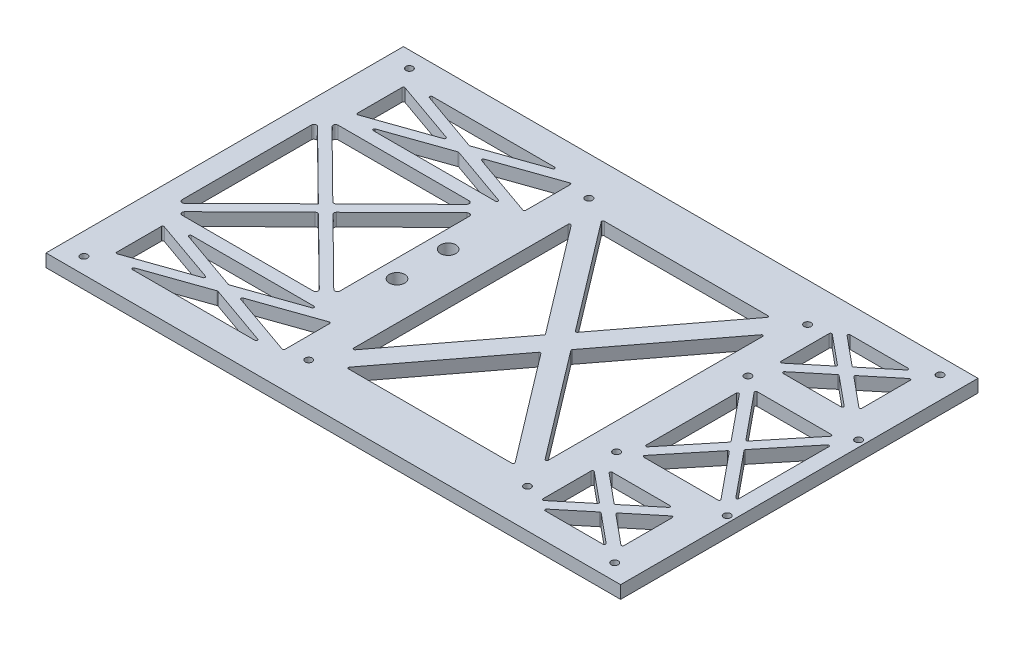
SolidWorks part; units mm, degrees
ref_plane "Front" through (0, 0, 0) normal (0, 0, 1) x (1, 0, 0)
ref_plane "Top" through (0, 0, 0) normal (0, 1, 0) x (1, 0, 0)
ref_plane "Right" through (0, 0, 0) normal (1, 0, 0) x (0, 0, -1)
sketch "batteryPackMountingHolesSketch" plane through (0, 0, 0) normal (0, 1, 0) x (1, 0, 0)
  line L0 (46, 0) -> (46, 116) construction
  line L1 (0, 0) -> (92, 0) construction
  line L2 (0, 0) -> (0, 116) construction
  line L3 (0, 116) -> (92, 116) construction
  line L4 (92, 0) -> (92, 116) construction
  line L5 (0, 58) -> (92, 58) construction
  circle A0 centre (3.25, 112.75) radius 1.375
  circle A1 centre (3.25, 3.25) radius 1.375
  circle A2 centre (88.75, 112.75) radius 1.375
  circle A3 centre (88.75, 3.25) radius 1.375
  dimension "D3" = 2.75
  dimension "D1" = 116
  dimension "D2" = 92
  dimension "D4" = 3.25
  dimension "D5" = 3.25
sketch "9VbatteryMountingHolesSketch" plane through (0, 0, 0) normal (0, 1, 0) x (1, 0, 0)
  line L0 (0, 58) -> (92, 58) construction
  line L1 (92, 28.575) -> (140.25, 28.575) construction
  line L2 (92, 28.575) -> (92, 87.425) construction
  line L3 (92, 87.425) -> (140.25, 87.425) construction
  line L4 (140.25, 28.575) -> (140.25, 87.425) construction
  line L5 (116.125, 28.575) -> (116.125, 87.425) construction
  line L6 (92, 58) -> (140.25, 58) construction
  line L7 (92, 0) -> (92, 116) construction
  circle A0 centre (94.5, 83.675) radius 1.375
  circle A1 centre (137.75, 83.675) radius 1.375
  circle A2 centre (94.5, 32.325) radius 1.375
  circle A3 centre (137.75, 32.325) radius 1.375
  point P5 (92, 58)
  dimension "D3" = 2.75
  dimension "D1" = 48.25
  dimension "D2" = 58.85
  dimension "D4" = 3.75
  dimension "D5" = 2.5
sketch "dualSwitchMountingHolesSketch" plane through (0, 0, 0) normal (0, 1, 0) x (1, 0, 0)
  line L0 (-7, 68) -> (-7, 48) construction
  line L1 (0, 58) -> (-14, 58) construction
  line L2 (-14, 77) -> (0, 77) construction
  line L3 (-14, 77) -> (-14, 39) construction
  line L4 (-14, 39) -> (0, 39) construction
  line L5 (0, 77) -> (0, 39) construction
  line L6 (0, 58) -> (92, 58) construction
  line L7 (0, 0) -> (0, 116) construction
  circle A0 centre (-7, 68) radius 3
  circle A1 centre (-7, 48) radius 3
  point P8 (-7, 58)
  point P11 (-7, 58)
  dimension "D1" = 6
  dimension "D2" = 20
  dimension "D3" = 14
  dimension "D4" = 9
sketch "Sketch4" plane through (0, 0, 0) normal (0, 1, 0) x (1, 0, 0)
  line L0 (-84.34, 58) -> (140.25, 58) construction
  line L1 (-84.34, -11.85) -> (140.25, -11.85)
  line L2 (-84.34, -11.85) -> (-84.34, 127.85)
  line L3 (-84.34, 127.85) -> (140.25, 127.85)
  line L4 (140.25, -11.85) -> (140.25, 127.85)
  line L5 (0, 58) -> (92, 58) construction
  line L6 (140.25, 28.575) -> (140.25, 87.425) construction
  dimension "D1" = 224.59
  dimension "D2" = 139.7
extrude "topChassisBase" add sketch "Sketch4" along normal blind 5
extrude "batteryPackMountingHoles" cut sketch "batteryPackMountingHolesSketch" along normal blind 7.5
extrude "9VbatteryMountingHoles" cut sketch "9VbatteryMountingHolesSketch" along normal blind 7.5
extrude "dualSwitchMountingHoles" cut sketch "dualSwitchMountingHolesSketch" along normal blind 7.5
sketch "Sketch5" plane through (0, 5, 0) normal (0, 1, 0) x (1, 0, 0)
  line L0 (-84.34, 58) -> (140.25, 58) construction
  line L1 (-84.34, 127.85) -> (-84.34, -11.85) construction
  line L2 (140.25, -11.85) -> (140.25, 127.85) construction
  line L3 (27.955, -11.85) -> (27.955, 127.85) construction
  line L4 (-84.34, -11.85) -> (140.25, -11.85) construction
  line L5 (140.25, 127.85) -> (-84.34, 127.85) construction
  circle A0 centre (-75.7725, 121.6) radius 1.375
  circle A1 centre (131.6825, 121.6) radius 1.375
  circle A2 centre (-75.7725, -5.6) radius 1.375
  circle A3 centre (131.6825, -5.6) radius 1.375
  dimension "D1" = 2.75
  dimension "D2" = 6.25
  dimension "D3" = 8.5675
extrude "bottomChassisMountingHoles" cut sketch "Sketch5" against normal through all
sketch "Sketch7" plane through (0, 5, 0) normal (0, 1, 0) x (1, 0, 0)
  line L0 (8.8981, 100.2077) -> (40.746, 58.3025)
  line L1 (13.634, 8.8025) -> (45.6019, 50.8655)
  line L2 (13.634, 107.1975) -> (45.6019, 65.1345)
  line L3 (8.8981, 15.7923) -> (40.746, 57.6975)
  line L4 (11.1846, 110.4203) -> (87.1846, 10.4203) construction
  line L5 (4.8154, 105.5797) -> (80.8154, 5.5797) construction
  line L6 (11.1846, 5.5797) -> (87.1846, 105.5797) construction
  line L7 (4.8154, 10.4203) -> (80.8154, 110.4203) construction
  line L8 (46.3981, 65.1345) -> (78.366, 107.1975)
  line L9 (46.3981, 50.8655) -> (78.366, 8.8025)
  line L10 (51.254, 57.6975) -> (83.1019, 15.7923)
  line L11 (51.254, 58.3025) -> (83.1019, 100.2077)
  line L12 (-7, 68) -> (-7, 48) construction
  line L13 (94.5, 83.675) -> (137.75, 83.675) construction
  line L14 (8, 108) -> (84, 8) construction
  line L15 (8, 8) -> (84, 108) construction
  line L16 (94.5, 83.675) -> (94.5, 32.325) construction
  line L17 (94.5, 32.325) -> (137.75, 32.325) construction
  line L18 (8, 8) -> (84, 8)
  line L19 (84, 8) -> (84, 108)
  line L20 (8, 108) -> (8, 8)
  line L21 (84, 108) -> (8, 108)
  line L22 (14.0321, 8) -> (77.9679, 8)
  line L23 (84, 16.0949) -> (84, 99.9051)
  line L24 (8, 99.9051) -> (8, 16.0949)
  line L25 (77.9679, 108) -> (14.0321, 108)
  line L26 (137.75, 83.675) -> (137.75, 32.325) construction
  line L28 (101.6375, 80.175) -> (130.6125, 80.175)
  line L29 (134.25, 75.6129) -> (134.25, 40.3871)
  line L30 (101.6375, 35.825) -> (130.6125, 35.825)
  line L31 (98, 75.6129) -> (98, 40.3871)
  line L32 (98, 80.175) -> (134.25, 35.825) construction
  line L33 (98, 35.825) -> (134.25, 80.175) construction
  line L34 (98.8871, 75.9294) -> (113.2833, 58.3164)
  line L35 (101.2504, 36.6414) -> (115.7379, 54.3661)
  line L36 (101.2504, 79.3586) -> (115.7379, 61.6339)
  line L37 (98.8871, 40.0706) -> (113.2833, 57.6836)
  line L38 (99.5485, 81.4407) -> (135.7985, 37.0907) construction
  line L39 (98, 80.175) -> (134.25, 80.175) construction
  line L40 (98, 80.175) -> (98, 35.825) construction
  line L41 (96.4515, 78.9093) -> (132.7015, 34.5593) construction
  line L42 (96.4515, 37.0907) -> (132.7015, 81.4407) construction
  line L43 (98, 35.825) -> (134.25, 35.825) construction
  line L44 (99.5485, 34.5593) -> (135.7985, 78.9093) construction
  line L45 (134.25, 80.175) -> (134.25, 35.825) construction
  line L46 (116.5121, 61.6339) -> (130.9996, 79.3586)
  line L47 (116.5121, 54.3661) -> (130.9996, 36.6414)
  line L48 (118.9667, 58.3164) -> (133.3629, 75.9294)
  line L49 (118.9667, 57.6836) -> (133.3629, 40.0706)
  line L50 (92, 87.425) -> (140.25, 87.425) construction
  line L51 (131.6825, 121.6) -> (92, 121.6) construction
  line L52 (131.6825, 121.6) -> (131.6825, 87.425) construction
  line L53 (131.6825, 87.425) -> (92, 87.425) construction
  line L54 (92, 121.6) -> (92, 87.425) construction
  line L55 (92, 0) -> (92, 116) construction
  line L56 (-84.34, 58) -> (-125.8248, 58) construction
  line L57 (123.1521, 117.6) -> (100.5304, 117.6)
  line L58 (96, 113.9441) -> (96, 95.0809)
  line L59 (123.1521, 91.425) -> (100.5304, 91.425)
  line L60 (127.6825, 113.9441) -> (127.6825, 95.0809)
  line L61 (96, 117.6) -> (127.6825, 91.425) construction
  line L62 (96, 91.425) -> (127.6825, 117.6) construction
  line L63 (96.8185, 114.3296) -> (108.2346, 104.898)
  line L64 (100.2119, 92.3105) -> (111.5228, 101.6551)
  line L65 (100.2119, 116.7145) -> (111.5228, 107.3699)
  line L66 (96.8185, 94.6954) -> (108.2346, 104.127)
  line L67 (94.7262, 92.9669) -> (126.4087, 119.1419) construction
  line L68 (96, 117.6) -> (96, 91.425) construction
  line L69 (127.6825, 91.425) -> (96, 91.425) construction
  line L70 (97.2738, 89.8831) -> (128.9563, 116.0581) construction
  line L71 (94.7262, 116.0581) -> (126.4087, 89.8831) construction
  line L72 (127.6825, 117.6) -> (127.6825, 91.425) construction
  line L73 (97.2738, 119.1419) -> (128.9563, 92.9669) construction
  line L74 (127.6825, 117.6) -> (96, 117.6) construction
  line L75 (115.4479, 104.898) -> (126.864, 114.3296)
  line L76 (115.4479, 104.127) -> (126.864, 94.6954)
  line L77 (112.1597, 107.3699) -> (123.4706, 116.7145)
  line L78 (112.1597, 101.6551) -> (123.4706, 92.3105)
  line L79 (115.4479, 11.102) -> (126.864, 1.6704)
  line L80 (115.4479, 11.873) -> (126.864, 21.3046)
  line L81 (127.6825, 2.0559) -> (127.6825, 20.9191)
  line L82 (100.2119, 23.6895) -> (111.5228, 14.3449)
  line L83 (123.1521, 24.575) -> (100.5304, 24.575)
  line L84 (112.1597, 14.3449) -> (123.4706, 23.6895)
  line L85 (96.8185, 1.6704) -> (108.2346, 11.102)
  line L86 (96.8185, 21.3046) -> (108.2346, 11.873)
  line L87 (96, 2.0559) -> (96, 20.9191)
  line L88 (123.1521, -1.6) -> (100.5304, -1.6)
  line L89 (112.1597, 8.6301) -> (123.4706, -0.7145)
  line L90 (100.2119, -0.7145) -> (111.5228, 8.6301)
  line L91 (-75.7725, 88.5) -> (-14, 88.5) construction
  line L92 (-75.7725, -5.6) -> (0, -5.6) construction
  line L93 (-75.7725, -5.6) -> (-75.7725, 27.5) construction
  line L95 (0, -5.6) -> (0, 27.5) construction
  line L96 (0, 0) -> (0, 116) construction
  line L97 (-5, 2.2253) -> (-5, 19.6747)
  line L98 (-61.8044, 22.5) -> (-13.9681, 22.5)
  line L99 (-70.7725, 2.2253) -> (-70.7725, 19.6747)
  line L100 (-61.8044, -0.6) -> (-13.9681, -0.6)
  line L101 (-70.7725, 22.5) -> (-5, -0.6) construction
  line L102 (-70.7725, -0.6) -> (-5, 22.5) construction
  line L103 (-70.1068, 20.1464) -> (-45.2651, 11.4218)
  line L104 (-61.97, 0.3718) -> (-38.0519, 8.772)
  line L105 (-61.97, 21.5282) -> (-38.0519, 13.128)
  line L106 (-70.1068, 1.7536) -> (-45.2651, 10.4782)
  line L107 (-70.1098, 24.387) -> (-4.3373, 1.287) construction
  line L108 (-70.7725, 22.5) -> (-5, 22.5) construction
  line L109 (-71.4352, 20.613) -> (-5.6627, -2.487) construction
  line L110 (-70.7725, -0.6) -> (-70.7725, 22.5) construction
  line L111 (-71.4352, 1.287) -> (-5.6627, 24.387) construction
  line L112 (-70.1098, -2.487) -> (-4.3373, 20.613) construction
  line L113 (-70.7725, -0.6) -> (-5, -0.6) construction
  line L114 (-5, -0.6) -> (-5, 22.5) construction
  line L115 (-37.7206, 13.128) -> (-13.8025, 21.5282)
  line L116 (-37.7206, 8.772) -> (-13.8025, 0.3718)
  line L117 (-30.5074, 10.4782) -> (-5.6657, 1.7536)
  line L118 (-30.5074, 11.4218) -> (-5.6657, 20.1464)
  line L119 (-61.97, 115.6282) -> (-38.0519, 107.228)
  line L120 (-37.7206, 107.228) -> (-13.8025, 115.6282)
  line L121 (-61.8044, 116.6) -> (-13.9681, 116.6)
  line L122 (-30.5074, 104.5782) -> (-5.6657, 95.8536)
  line L123 (-5, 113.7747) -> (-5, 96.3253)
  line L124 (-30.5074, 105.5218) -> (-5.6657, 114.2464)
  line L125 (-61.97, 94.4718) -> (-38.0519, 102.872)
  line L126 (-61.8044, 93.5) -> (-13.9681, 93.5)
  line L127 (-37.7206, 102.872) -> (-13.8025, 94.4718)
  line L128 (-70.1068, 114.2464) -> (-45.2651, 105.5218)
  line L129 (-70.1068, 95.8536) -> (-45.2651, 104.5782)
  line L130 (-70.7725, 113.7747) -> (-70.7725, 96.3253)
  line L138 (0, 88.5) -> (-75.7725, 88.5) construction
  line L139 (-75.7725, 27.5) -> (0, 27.5) construction
  line L144 (0, 27.5) -> (-75.7725, 27.5) construction
  line L145 (-75.7725, 88.5) -> (-75.7725, 27.5) construction
  line L146 (-75.7725, 27.5) -> (-14, 27.5) construction
  line L147 (-14, 88.5) -> (-14, 27.5) construction
  line L148 (-14, 88.5) -> (-75.7725, 27.5) construction
  line L149 (-75.7725, 88.5) -> (-14, 27.5) construction
  line L150 (-18.5796, 86.7885) -> (-44.1836, 61.5047)
  line L151 (-74.0699, 84.0079) -> (-47.7326, 58)
  line L155 (-15.7026, 84.0079) -> (-41.3193, 58.7115)
  line L156 (-71.1929, 86.7885) -> (-45.5889, 61.5047)
  line L158 (-75.7725, 121.6) -> (-75.7725, 88.5) construction
  line L160 (-75.7725, 121.6) -> (0, 121.6) construction
  line L161 (0, 121.6) -> (0, 88.5) construction
  line L162 (-19.2823, 88.5) -> (-70.4902, 88.5)
  line L163 (-75.7725, 83.2963) -> (-75.7725, 32.7037)
  line L164 (-70.4902, 27.5) -> (-19.2823, 27.5)
  line L166 (-14, 83.2963) -> (-14, 32.7037)
  line L168 (-15.4053, 89.9231) -> (-77.1778, 28.9231) construction
  line L169 (-12.5947, 87.0769) -> (-74.3672, 26.0769) construction
  line L170 (-74.3672, 89.9231) -> (-12.5947, 28.9231) construction
  line L171 (-77.1778, 87.0769) -> (-15.4053, 26.0769) construction
  line L172 (-41.3193, 57.2885) -> (-15.7026, 31.9921)
  line L173 (-47.7326, 58) -> (-74.0699, 31.9921)
  line L174 (-45.5889, 54.4953) -> (-71.1929, 29.2115)
  line L175 (-44.1836, 54.4953) -> (-18.5796, 29.2115)
  arc A0 (96.8185, 114.3296) -> (96, 113.9441) centre (96.5, 113.9441) ccw
  arc A1 (108.2346, 104.898) -> (108.2346, 104.127) centre (107.9161, 104.5125) cw
  arc A2 (123.4706, 116.7145) -> (123.1521, 117.6) centre (123.1521, 117.1) ccw
  arc A3 (100.2119, 116.7145) -> (100.5304, 117.6) centre (100.5304, 117.1) cw
  arc A4 (111.5228, 107.3699) -> (112.1597, 107.3699) centre (111.8413, 107.7553) ccw
  arc A5 (126.864, 114.3296) -> (127.6825, 113.9441) centre (127.1825, 113.9441) cw
  arc A6 (115.4479, 104.898) -> (115.4479, 104.127) centre (115.7664, 104.5125) ccw
  arc A7 (127.6825, 95.0809) -> (126.864, 94.6954) centre (127.1825, 95.0809) cw
  arc A8 (123.4706, 92.3105) -> (123.1521, 91.425) centre (123.1521, 91.925) cw
  arc A9 (112.1597, 101.6551) -> (111.5228, 101.6551) centre (111.8413, 101.2697) ccw
  arc A10 (100.5304, 91.425) -> (100.2119, 92.3105) centre (100.5304, 91.925) cw
  arc A11 (96.8185, 94.6954) -> (96, 95.0809) centre (96.5, 95.0809) cw
  arc A12 (115.4479, 11.102) -> (115.4479, 11.873) centre (115.7664, 11.4875) cw
  arc A13 (126.864, 1.6704) -> (127.6825, 2.0559) centre (127.1825, 2.0559) ccw
  arc A14 (127.6825, 20.9191) -> (126.864, 21.3046) centre (127.1825, 20.9191) ccw
  arc A15 (100.5304, 24.575) -> (100.2119, 23.6895) centre (100.5304, 24.075) ccw
  arc A16 (123.4706, 23.6895) -> (123.1521, 24.575) centre (123.1521, 24.075) ccw
  arc A17 (112.1597, 14.3449) -> (111.5228, 14.3449) centre (111.8413, 14.7303) cw
  arc A18 (108.2346, 11.102) -> (108.2346, 11.873) centre (107.9161, 11.4875) ccw
  arc A19 (96.8185, 1.6704) -> (96, 2.0559) centre (96.5, 2.0559) cw
  arc A20 (96.8185, 21.3046) -> (96, 20.9191) centre (96.5, 20.9191) ccw
  arc A21 (123.4706, -0.7145) -> (123.1521, -1.6) centre (123.1521, -1.1) cw
  arc A22 (100.2119, -0.7145) -> (100.5304, -1.6) centre (100.5304, -1.1) ccw
  arc A23 (111.5228, 8.6301) -> (112.1597, 8.6301) centre (111.8413, 8.2447) cw
  arc A24 (98, 75.6129) -> (98.8871, 75.9294) centre (98.5, 75.6129) cw
  arc A25 (113.2833, 57.6836) -> (113.2833, 58.3164) centre (112.8961, 58) ccw
  arc A26 (98.8871, 40.0706) -> (98, 40.3871) centre (98.5, 40.3871) cw
  arc A27 (101.2504, 79.3586) -> (101.6375, 80.175) centre (101.6375, 79.675) cw
  arc A28 (116.5121, 61.6339) -> (115.7379, 61.6339) centre (116.125, 61.9503) cw
  arc A29 (130.9996, 79.3586) -> (130.6125, 80.175) centre (130.6125, 79.675) ccw
  arc A30 (134.25, 75.6129) -> (133.3629, 75.9294) centre (133.75, 75.6129) ccw
  arc A31 (118.9667, 58.3164) -> (118.9667, 57.6836) centre (119.3539, 58) ccw
  arc A32 (133.3629, 40.0706) -> (134.25, 40.3871) centre (133.75, 40.3871) ccw
  arc A33 (130.9996, 36.6414) -> (130.6125, 35.825) centre (130.6125, 36.325) cw
  arc A34 (116.5121, 54.3661) -> (115.7379, 54.3661) centre (116.125, 54.0497) ccw
  arc A35 (101.6375, 35.825) -> (101.2504, 36.6414) centre (101.6375, 36.325) cw
  arc A36 (78.366, 107.1975) -> (77.9679, 108) centre (77.9679, 107.5) ccw
  arc A37 (46.3981, 65.1345) -> (45.6019, 65.1345) centre (46, 65.437) cw
  arc A38 (13.634, 107.1975) -> (14.0321, 108) centre (14.0321, 107.5) cw
  arc A39 (8, 99.9051) -> (8.8981, 100.2077) centre (8.5, 99.9051) cw
  arc A40 (40.746, 57.6975) -> (40.746, 58.3025) centre (40.3479, 58) ccw
  arc A41 (8.8981, 15.7923) -> (8, 16.0949) centre (8.5, 16.0949) cw
  arc A42 (83.1019, 100.2077) -> (84, 99.9051) centre (83.5, 99.9051) cw
  arc A43 (51.254, 57.6975) -> (51.254, 58.3025) centre (51.6521, 58) cw
  arc A44 (83.1019, 15.7923) -> (84, 16.0949) centre (83.5, 16.0949) ccw
  arc A45 (78.366, 8.8025) -> (77.9679, 8) centre (77.9679, 8.5) cw
  arc A46 (46.3981, 50.8655) -> (45.6019, 50.8655) centre (46, 50.563) ccw
  arc A47 (14.0321, 8) -> (13.634, 8.8025) centre (14.0321, 8.5) cw
  arc A48 (-61.97, 21.5282) -> (-61.8044, 22.5) centre (-61.8044, 22) cw
  arc A49 (-13.8025, 21.5282) -> (-13.9681, 22.5) centre (-13.9681, 22) ccw
  arc A50 (-37.7206, 13.128) -> (-38.0519, 13.128) centre (-37.8862, 13.5997) cw
  arc A51 (-5, 19.6747) -> (-5.6657, 20.1464) centre (-5.5, 19.6747) ccw
  arc A52 (-30.5074, 10.4782) -> (-30.5074, 11.4218) centre (-30.3418, 10.95) cw
  arc A53 (-5, 2.2253) -> (-5.6657, 1.7536) centre (-5.5, 2.2253) cw
  arc A54 (-13.8025, 0.3718) -> (-13.9681, -0.6) centre (-13.9681, -0.1) cw
  arc A55 (-38.0519, 8.772) -> (-37.7206, 8.772) centre (-37.8863, 8.3003) cw
  arc A56 (-61.97, 0.3718) -> (-61.8044, -0.6) centre (-61.8044, -0.1) ccw
  arc A57 (-70.1068, 1.7536) -> (-70.7725, 2.2253) centre (-70.2725, 2.2253) cw
  arc A58 (-45.2651, 10.4782) -> (-45.2651, 11.4218) centre (-45.4307, 10.95) ccw
  arc A59 (-70.1068, 20.1464) -> (-70.7725, 19.6747) centre (-70.2725, 19.6747) ccw
  arc A60 (-38.0519, 107.228) -> (-37.7206, 107.228) centre (-37.8863, 107.6997) ccw
  arc A61 (-13.8025, 115.6282) -> (-13.9681, 116.6) centre (-13.9681, 116.1) ccw
  arc A62 (-61.97, 115.6282) -> (-61.8044, 116.6) centre (-61.8044, 116.1) cw
  arc A63 (-5, 96.3253) -> (-5.6657, 95.8536) centre (-5.5, 96.3253) cw
  arc A64 (-30.5074, 105.5218) -> (-30.5074, 104.5782) centre (-30.3418, 105.05) ccw
  arc A65 (-5, 113.7747) -> (-5.6657, 114.2464) centre (-5.5, 113.7747) ccw
  arc A66 (-61.97, 94.4718) -> (-61.8044, 93.5) centre (-61.8044, 94) ccw
  arc A67 (-13.8025, 94.4718) -> (-13.9681, 93.5) centre (-13.9681, 94) cw
  arc A68 (-37.7206, 102.872) -> (-38.0519, 102.872) centre (-37.8863, 102.4003) ccw
  arc A69 (-45.2651, 105.5218) -> (-45.2651, 104.5782) centre (-45.4307, 105.05) cw
  arc A70 (-70.1068, 114.2464) -> (-70.7725, 113.7747) centre (-70.2725, 113.7747) ccw
  arc A71 (-70.1068, 95.8536) -> (-70.7725, 96.3253) centre (-70.2725, 96.3253) cw
  circle A72 centre (-7, 48) radius 3 construction
  circle A73 centre (-7, 68) radius 3 construction
  circle A74 centre (-7, 48) radius 3 construction
  circle A75 centre (-7, 68) radius 3 construction
  arc A76 (-70.4902, 88.5) -> (-71.1929, 86.7885) centre (-70.4902, 87.5) ccw
  arc A77 (-75.7725, 83.2963) -> (-74.0699, 84.0079) centre (-74.7725, 83.2963) cw
  arc A78 (-75.7725, 32.7037) -> (-74.0699, 31.9921) centre (-74.7725, 32.7037) ccw
  arc A79 (-70.4902, 27.5) -> (-71.1929, 29.2115) centre (-70.4902, 28.5) cw
  arc A80 (-45.5889, 54.4953) -> (-44.1836, 54.4953) centre (-44.8863, 53.7838) cw
  arc A81 (-19.2823, 27.5) -> (-18.5796, 29.2115) centre (-19.2823, 28.5) ccw
  arc A82 (-14, 32.7037) -> (-15.7026, 31.9921) centre (-15, 32.7037) cw
  arc A83 (-41.3193, 57.2885) -> (-41.3193, 58.7115) centre (-40.6167, 58) cw
  arc A84 (-45.5889, 61.5047) -> (-44.1836, 61.5047) centre (-44.8863, 62.2162) ccw
  arc A85 (-19.2823, 88.5) -> (-18.5796, 86.7885) centre (-19.2823, 87.5) cw
  arc A86 (-14, 83.2963) -> (-15.7026, 84.0079) centre (-15, 83.2963) ccw
  point P101 (111.8413, 107.1068)
  point P106 (114.9814, 104.5125)
  point P169 (118.7081, 58)
  point P194 (51.0241, 58)
  point P246 (-31.8507, 10.95)
  point P325 (-72.9261, 88.5)
  point P328 (-75.7725, 85.6892)
  point P331 (-75.7725, 30.3108)
  point P334 (-72.9261, 27.5)
  point P337 (-44.8863, 55.1892)
  point P340 (-16.8464, 27.5)
  point P343 (-14, 30.3108)
  point P350 (-16.8464, 88.5)
  point P353 (-14, 85.6892)
  dimension "D10" = 0.5
  dimension "D11" = 0.5
  dimension "D12" = 0.5
  dimension "D16" = 0.5
  dimension "D20" = 2
  dimension "D21" = 1
  dimension "D17" = 61
  dimension "D18" = 7
  dimension "D1" = 8
  dimension "D2" = 4
  dimension "D3" = 4
  dimension "D4" = 3.5
  dimension "D5" = 2
  dimension "D6" = 2
  dimension "D7" = 4
  dimension "D8" = 2
  dimension "D9" = 2
  dimension "D13" = 5
  dimension "D14" = 2
  dimension "D15" = 2
  dimension "D19" = 2
extrude "weightReduction" cut sketch "Sketch7" against normal through all
